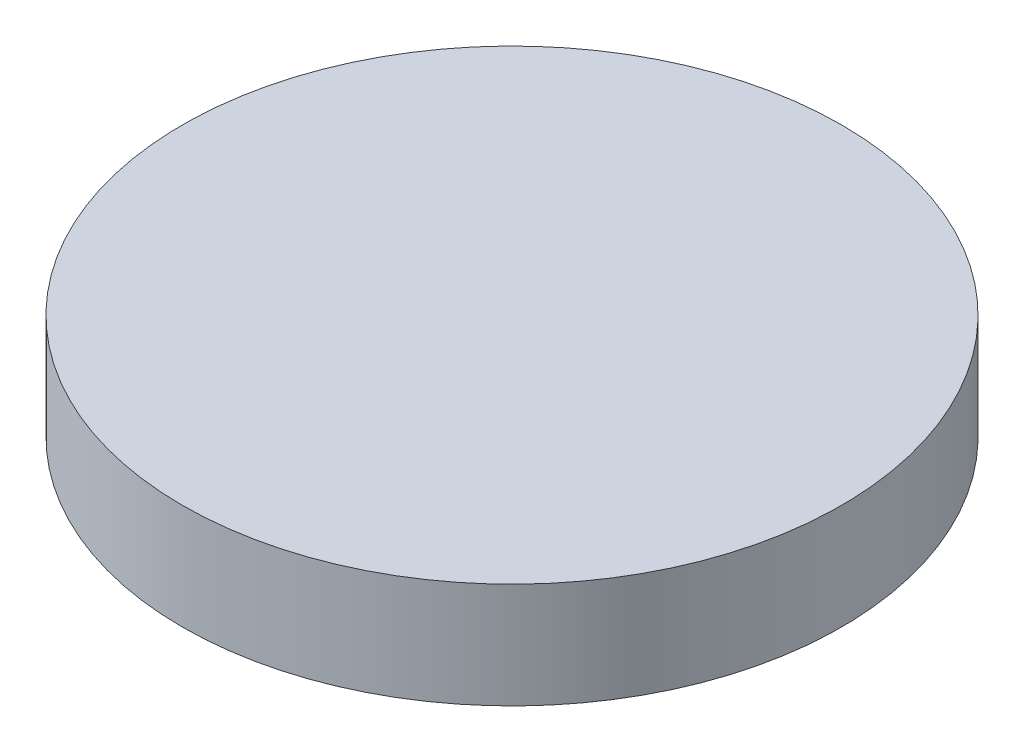
SolidWorks part; units mm, degrees
ref_plane "Спереди" through (0, 0, 0) normal (0, 0, 1) x (1, 0, 0)
ref_plane "Сверху" through (0, 0, 0) normal (0, 1, 0) x (1, 0, 0)
ref_plane "Справа" through (0, 0, 0) normal (1, 0, 0) x (0, 0, -1)
sketch "Эскиз1" plane through (0, 0, 0) normal (0, 1, 0) x (1, 0, 0)
  circle A0 centre (0, 0) radius 10
  dimension "D1" = 20
extrude "Бобышка-Вытянуть1" add sketch "Эскиз1" along normal blind 3.2
